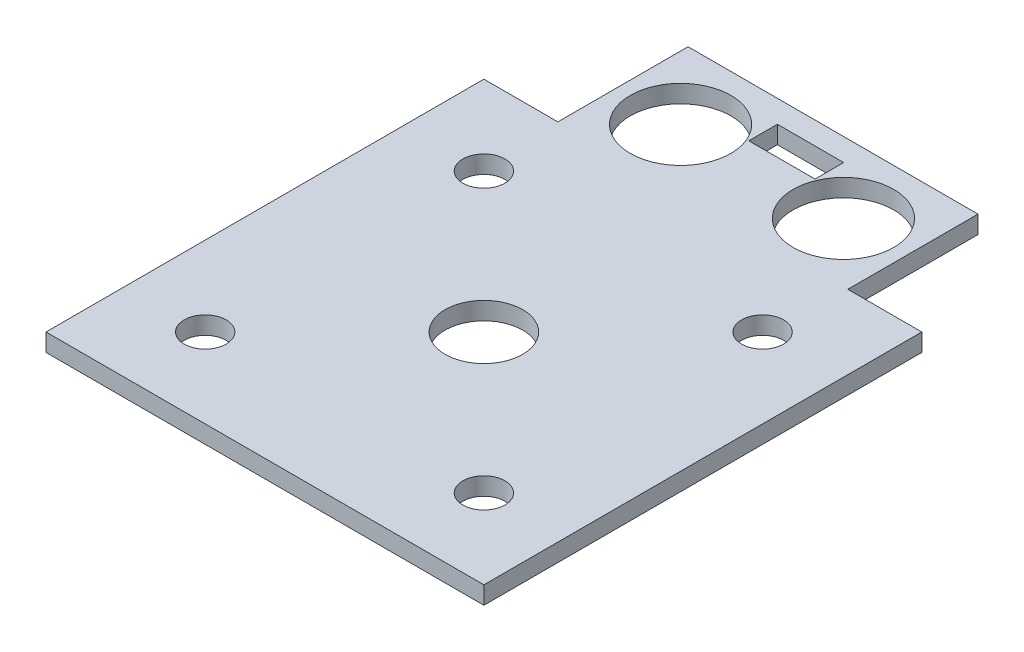
SolidWorks part; units mm, degrees
ref_plane "Front Plane" through (0, 0, 0) normal (0, 0, 1) x (1, 0, 0)
ref_plane "Top Plane" through (0, 0, 0) normal (0, 1, 0) x (1, 0, 0)
ref_plane "Right Plane" through (0, 0, 0) normal (1, 0, 0) x (0, 0, -1)
sketch "Sketch1" plane through (0, 0, 0) normal (0, 1, 0) x (1, 0, 0)
  circle A0 centre (0, 0) radius 20
  circle A1 centre (0, 0) radius 21
  dimension "D1" = 40
  dimension "D2" = 42
extrude "Boss-Extrude1" add sketch "Sketch1" along normal blind 3.5
ref_plane "Plane1" through (0, 3.5, 0) normal (0, 1, 0) x (1, 0, 0)
sketch "Sketch2" plane through (0, 3.5, 0) normal (0, 1, 0) x (1, 0, 0)
  line L0 (-23.55, 0) -> (23.55, 0) construction
  line L1 (-37, -37) -> (37, -37)
  line L2 (-37, -37) -> (-37, 37)
  line L3 (-37, 37) -> (37, 37)
  line L4 (37, -37) -> (37, 37)
  line L5 (-37, -37) -> (37, 37) construction
  line L6 (-37, 37) -> (37, -37) construction
  line L7 (-28.2, -28.2) -> (28.2, -28.2) construction
  line L8 (-28.2, -28.2) -> (-28.2, 28.2) construction
  line L9 (-28.2, 28.2) -> (28.2, 28.2) construction
  line L10 (28.2, -28.2) -> (28.2, 28.2) construction
  line L11 (-28.2, -28.2) -> (28.2, 28.2) construction
  line L12 (-28.2, 28.2) -> (28.2, -28.2) construction
  line L13 (-23.55, 28.2) -> (-23.55, 23.55) construction
  line L14 (-23.55, 23.55) -> (-28.2, 23.55) construction
  line L15 (0, 28.2) -> (0, -28.2) construction
  line L16 (0, 37) -> (0, 57) construction
  line L17 (-22.5, 57) -> (22.5, 57) construction
  line L18 (-22.5, 57) -> (-22.5, 37) construction
  line L19 (22.5, 57) -> (22.5, 37) construction
  line L20 (0, 57) -> (0, 54.5) construction
  line L21 (-4.9, 54.5) -> (4.9, 54.5) construction
  line L22 (-4.9, 54.5) -> (-4.9, 51.06) construction
  line L23 (-4.9, 51.06) -> (4.9, 51.06) construction
  line L24 (4.9, 51.06) -> (4.9, 54.5) construction
  line L25 (-24.5, 37) -> (-24.5, 59)
  line L26 (-24.5, 59) -> (24.5, 59)
  line L27 (24.5, 59) -> (24.5, 37)
  line L28 (-13.76, 47) -> (13.76, 47) construction
  line L29 (-5.6, 55.2) -> (5.6, 55.2)
  line L31 (5.6, 50.36) -> (-5.6, 50.36)
  line L32 (-5.6, 50.36) -> (-5.6, 55.2)
  line L33 (5.6, 50.36) -> (5.6, 55.2)
  circle A0 centre (-23.55, 23.55) radius 2.55 construction
  circle A1 centre (23.55, 23.55) radius 2.55 construction
  circle A2 centre (23.55, -23.55) radius 2.55 construction
  circle A3 centre (-23.55, -23.55) radius 2.55 construction
  circle A4 centre (0, 0) radius 5.5563 construction
  circle A5 centre (13.76, 47) radius 7.5 construction
  circle A6 centre (-13.76, 47) radius 7.5 construction
  circle A7 centre (-13.76, 47) radius 8.5
  circle A8 centre (13.76, 47) radius 8.5
  circle A9 centre (0, 0) radius 6.55
  circle A10 centre (-23.55, 23.55) radius 3.55
  circle A11 centre (23.55, 23.55) radius 3.55
  circle A12 centre (23.55, -23.55) radius 3.55
  circle A13 centre (-23.55, -23.55) radius 3.55
  point P0 (0, 0)
  point P5 (0, 0)
  point P15 (0, 0)
  point P34 (0, 57)
  point P40 (0, 54.5)
  point P49 (0, 47)
  point P56 (0, 50.36)
  point P59 (0, 55.2)
  dimension "D4" = 5.1
  dimension "D5" = 11.1125
  dimension "D15" = 15
  dimension "D16" = 17
  dimension "D17" = 0.7
  dimension "D20" = 13.1
  dimension "D21" = 7.1
  dimension "D1" = 74
  dimension "D2" = 56.4
  dimension "D3" = 47.1
  dimension "D6" = 20
  dimension "D7" = 45
  dimension "D8" = 2.5
  dimension "D9" = 9.8
  dimension "D10" = 3.44
  dimension "D11" = 2
  dimension "D12" = 2
  dimension "D13" = 2
  dimension "D14" = 27.52
  dimension "D18" = 0.7
  dimension "D19" = 0.7
extrude "Boss-Extrude2" add sketch "Sketch2" along normal blind 3 contours L1 L4 L3 L2 A4 A1 A0 A2 A3 | L27 L26 L25 L3 A8 A7 L33 L31 L32 L29
